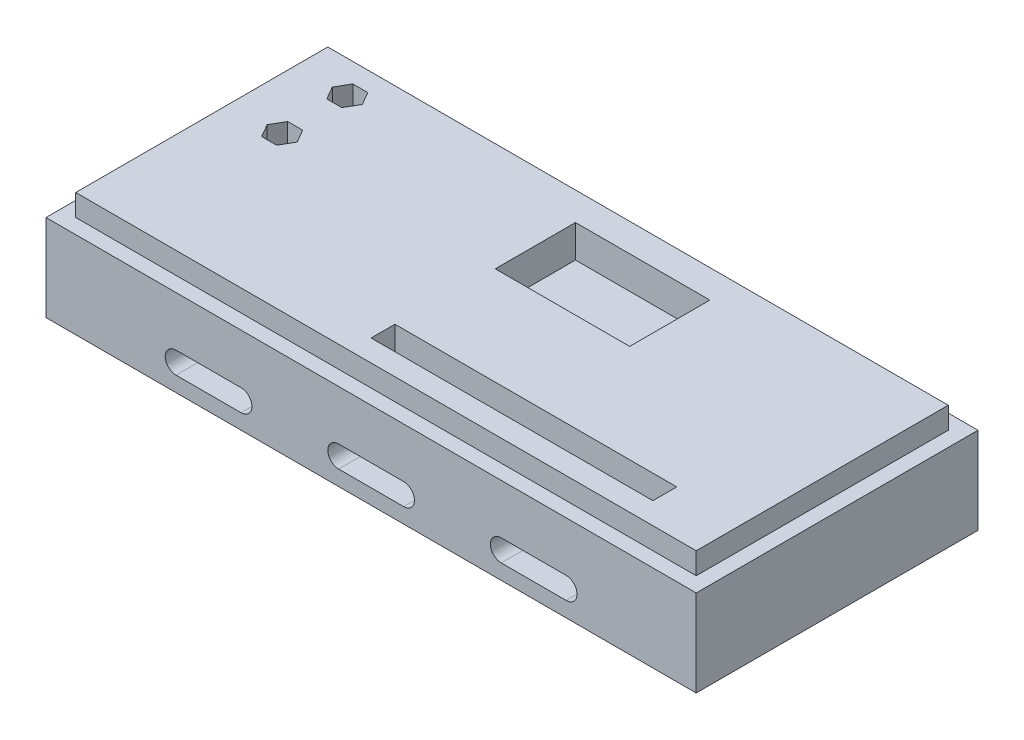
SolidWorks part; units mm, degrees
ref_plane "Front Plane" through (0, 0, 0) normal (0, 0, 1) x (1, 0, 0)
ref_plane "Top Plane" through (0, 0, 0) normal (0, 1, 0) x (1, 0, 0)
ref_plane "Right Plane" through (0, 0, 0) normal (1, 0, 0) x (0, 0, -1)
sketch "Sketch1" plane through (0, 0, 0) normal (0, 1, 0) x (1, 0, 0)
  line L1 (-75, -32.5) -> (75, -32.5)
  line L2 (-75, -32.5) -> (-75, 32.5)
  line L3 (-75, 32.5) -> (75, 32.5)
  line L4 (75, -32.5) -> (75, 32.5)
  line L5 (-75, -32.5) -> (75, 32.5) construction
  line L6 (-75, 32.5) -> (75, -32.5) construction
  point P1 (0, 0)
  dimension "D1" = 150
  dimension "D2" = 65
extrude "Boss-Extrude1" add sketch "Sketch1" along normal blind 20
sketch "Sketch2" plane through (0, 0, 32.5) normal (0, 0, 1) x (1, 0, 0)
  line L0 (0, 0) -> (0, 20) construction
  line L1 (-75, 20) -> (75, 20) construction
  line L2 (0, 10) -> (-75, 10) construction
  line L3 (-75, 20) -> (-75, 0) construction
  line L4 (0, 10) -> (75, 10) construction
  line L5 (-45, 6) -> (-30, 6) construction
  line L6 (-37.5, 10) -> (-37.5, 0) construction
  line L7 (35.75, 0) -> (-35.75, 0) construction
  line L8 (75, 20) -> (75, 0) construction
  line L9 (37.5, 10) -> (37.5, 0) construction
  line L10 (-7.5, 6) -> (7.5, 6) construction
  line L11 (-7.5, 8.5) -> (7.5, 8.5)
  line L12 (-7.5, 3.5) -> (7.5, 3.5)
  line L13 (-45, 8.5) -> (-30, 8.5)
  line L14 (-45, 3.5) -> (-30, 3.5)
  line L15 (30, 6) -> (45, 6) construction
  line L16 (30, 8.5) -> (45, 8.5)
  line L17 (30, 3.5) -> (45, 3.5)
  arc A0 (-7.5, 8.5) -> (-7.5, 3.5) centre (-7.5, 6) ccw
  arc A1 (7.5, 3.5) -> (7.5, 8.5) centre (7.5, 6) ccw
  arc A2 (-45, 8.5) -> (-45, 3.5) centre (-45, 6) ccw
  arc A3 (-30, 3.5) -> (-30, 8.5) centre (-30, 6) ccw
  arc A4 (30, 8.5) -> (30, 3.5) centre (30, 6) ccw
  arc A5 (45, 3.5) -> (45, 8.5) centre (45, 6) ccw
  point P20 (0, 6)
  point P29 (-37.5, 6)
  point P37 (37.5, 6)
  dimension "D1" = 15
  dimension "D2" = 5
  dimension "D3" = 3.5
  dimension "D4" = 15
  dimension "D5" = 5
  dimension "D6" = 3.5
  dimension "D7" = 15
  dimension "D8" = 5
  dimension "D9" = 3.5
extrude "Cut-Extrude1" cut sketch "Sketch2" against normal through all
sketch "Sketch3" plane through (0, 20, 0) normal (0, 1, 0) x (1, 0, 0)
  line L1 (-71.571, -29.071) -> (71.571, -29.071)
  line L2 (-71.571, -29.071) -> (-71.571, 29.071)
  line L3 (-71.571, 29.071) -> (71.571, 29.071)
  line L4 (71.571, -29.071) -> (71.571, 29.071)
  line L5 (-71.571, -29.071) -> (71.571, 29.071) construction
  line L6 (-71.571, 29.071) -> (71.571, -29.071) construction
  line L7 (-75, 32.5) -> (-75, -32.5) construction
  line L8 (75, 32.5) -> (-75, 32.5) construction
  point P0 (0, 0)
  dimension "D1" = 3.429
  dimension "D2" = 3.429
extrude "Boss-Extrude2" add sketch "Sketch3" along normal blind 5
sketch "Sketch4" plane through (0, 25, 0) normal (0, 1, 0) x (1, 0, 0)
  line L0 (-59.571, 21.571) -> (-59.571, 6.551) construction
  line L1 (71.571, 29.071) -> (-71.571, 29.071) construction
  line L2 (-71.571, 29.071) -> (-71.571, -29.071) construction
  line L4 (-61.3031, 24.571) -> (-63.0351, 21.571)
  line L5 (-63.0351, 21.571) -> (-61.3031, 18.571)
  line L6 (-61.3031, 18.571) -> (-57.8389, 18.571)
  line L7 (-57.8389, 18.571) -> (-56.1069, 21.571)
  line L8 (-56.1069, 21.571) -> (-57.8389, 24.571)
  line L9 (-57.8389, 24.571) -> (-61.3031, 24.571)
  line L10 (-61.3031, 9.551) -> (-63.0351, 6.551)
  line L11 (-63.0351, 6.551) -> (-61.3031, 3.551)
  line L12 (-61.3031, 3.551) -> (-57.8389, 3.551)
  line L13 (-57.8389, 3.551) -> (-56.1069, 6.551)
  line L14 (-56.1069, 6.551) -> (-57.8389, 9.551)
  line L15 (-57.8389, 9.551) -> (-61.3031, 9.551)
  circle A2 centre (-59.571, 21.571) radius 3 construction
  circle A3 centre (-59.571, 6.551) radius 3 construction
  dimension "D3" = 6
  dimension "D4" = 6
  dimension "D1" = 15.02
  dimension "D2" = 7.5
  dimension "D5" = 12
sketch "Sketch5" plane through (0, 25, 0) normal (0, 1, 0) x (1, 0, 0)
  line L1 (-61.591, 4.541) -> (-29.841, 4.541)
  line L2 (-61.591, 4.541) -> (-61.591, 23.591)
  line L3 (-61.591, 23.591) -> (-29.841, 23.591)
  line L4 (-29.841, 4.541) -> (-29.841, 23.591)
  line L5 (-61.591, 4.541) -> (-29.841, 23.591) construction
  line L6 (-61.591, 23.591) -> (-29.841, 4.541) construction
  point P0 (-45.716, 14.066)
  dimension "D3" = 2.02
  dimension "D1" = 19.05
  dimension "D2" = 31.75
  dimension "D4" = 2.02
extrude "Cut-Extrude2" cut sketch "Sketch4" against normal blind 6.5
sketch "Sketch6" plane through (0, 25, 0) normal (0, 1, 0) x (1, 0, 0)
  line L0 (-71.571, -29.071) -> (71.571, -29.071) construction
  line L1 (-8.429, -24.071) -> (56.571, -24.071)
  line L2 (-8.429, -24.071) -> (-8.429, -18.571)
  line L3 (-8.429, -18.571) -> (56.571, -18.571)
  line L4 (56.571, -24.071) -> (56.571, -18.571)
  line L5 (-8.429, -24.071) -> (56.571, -18.571) construction
  line L6 (-8.429, -18.571) -> (56.571, -24.071) construction
  line L7 (71.571, -29.071) -> (71.571, 29.071) construction
  point P0 (24.071, -21.321)
  dimension "D1" = 5.5
  dimension "D2" = 65
  dimension "D3" = 5
  dimension "D4" = 15
extrude "Cut-Extrude3" cut sketch "Sketch6" against normal blind 10
sketch "Sketch7" plane through (0, 25, 0) normal (0, 1, 0) x (1, 0, 0)
  line L0 (71.571, 29.071) -> (-71.571, 29.071) construction
  line L1 (-7.929, 4.071) -> (23.071, 4.071)
  line L2 (-7.929, 4.071) -> (-7.929, 22.571)
  line L3 (-7.929, 22.571) -> (23.071, 22.571)
  line L4 (23.071, 4.071) -> (23.071, 22.571)
  line L5 (-7.929, 4.071) -> (23.071, 22.571) construction
  line L6 (-7.929, 22.571) -> (23.071, 4.071) construction
  line L7 (71.571, -29.071) -> (71.571, 29.071) construction
  point P0 (7.571, 13.321)
  dimension "D1" = 31
  dimension "D2" = 18.5
  dimension "D3" = 6.5
  dimension "D4" = 48.5
extrude "Cut-Extrude4" cut sketch "Sketch7" against normal blind 7.5
